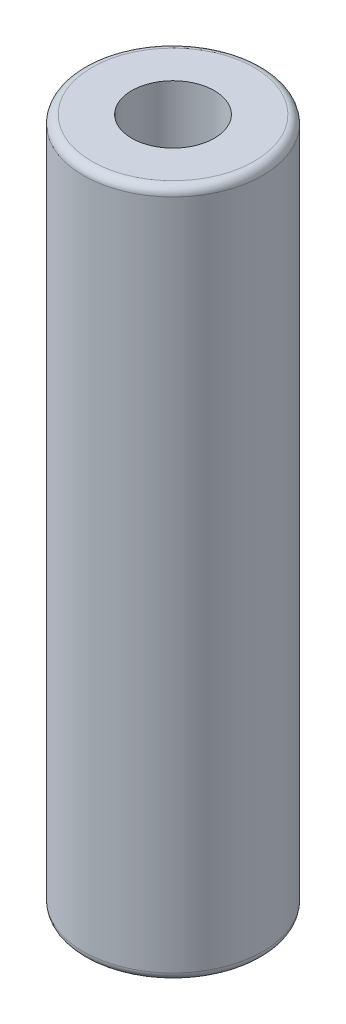
SolidWorks part; units mm, degrees
ref_plane "Plano frontal" through (0, 0, 0) normal (0, 0, 1) x (1, 0, 0)
ref_plane "Plano superior" through (0, 0, 0) normal (0, 1, 0) x (1, 0, 0)
ref_plane "Plano direito" through (0, 0, 0) normal (1, 0, 0) x (0, 0, -1)
sketch "Esboço1" plane through (0, 0, 0) normal (0, 1, 0) x (1, 0, 0)
  circle A0 centre (0, 0) radius 3.25
  dimension "D1" = 6.5
extrude "Ressalto-extrusão1" add sketch "Esboço1" along normal blind 25
sketch "Esboço2" plane through (0, 25, 0) normal (0, 1, 0) x (1, 0, 0)
  circle A0 centre (0, 0) radius 1.5
  dimension "D1" = 3
extrude "Corte-extrusão1" cut sketch "Esboço2" against normal through all
fillet "Filete1" radius 0.3 2 edges at (0, 0, 3.25) (0, 25, 3.25)
